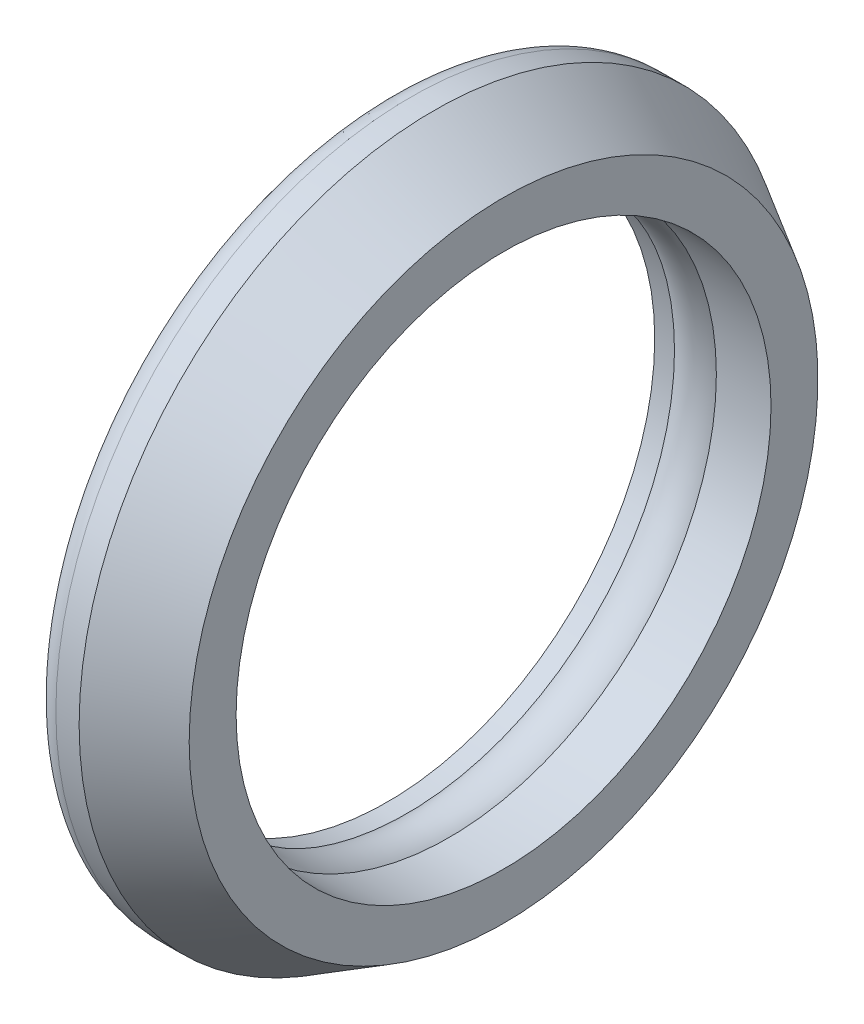
SolidWorks part; units mm, degrees
ref_plane "Front" through (0, 0, 0) normal (0, 0, 1) x (1, 0, 0)
ref_plane "Top" through (0, 0, 0) normal (0, 1, 0) x (1, 0, 0)
ref_plane "Right" through (0, 0, 0) normal (1, 0, 0) x (0, 0, -1)
sketch "Sketch1" plane through (0, 0, 0) normal (0, 0, 1) x (1, 0, 0)
  line L0 (0, 11.5) -> (0, 15.25)
  line L1 (0, 15.25) -> (2, 15.25)
  line L4 (5, 13.5179) -> (5, 11.5)
  line L6 (0, 0) -> (28.7571, 0) construction
  line L7 (2, 15.25) -> (5, 13.5179)
  line L12 (0, 11.5) -> (0.85, 11.5)
  line L13 (1.75, 11.5) -> (1.75, 14.3773) construction
  line L15 (2.65, 11.5) -> (5, 11.5)
  arc A0 (0.85, 11.5) -> (2.65, 11.5) centre (1.75, 12.7) ccw
  dimension "D6" = 3
  dimension "D1" = 30.5
  dimension "D3" = 5
  dimension "D4" = 2
  dimension "D5" = 60
revolve "Revolve1" add sketch "Sketch1" angle 360 about L6
fillet "Fillet1" radius 1 1 edges at (0, 0, 15.25)
